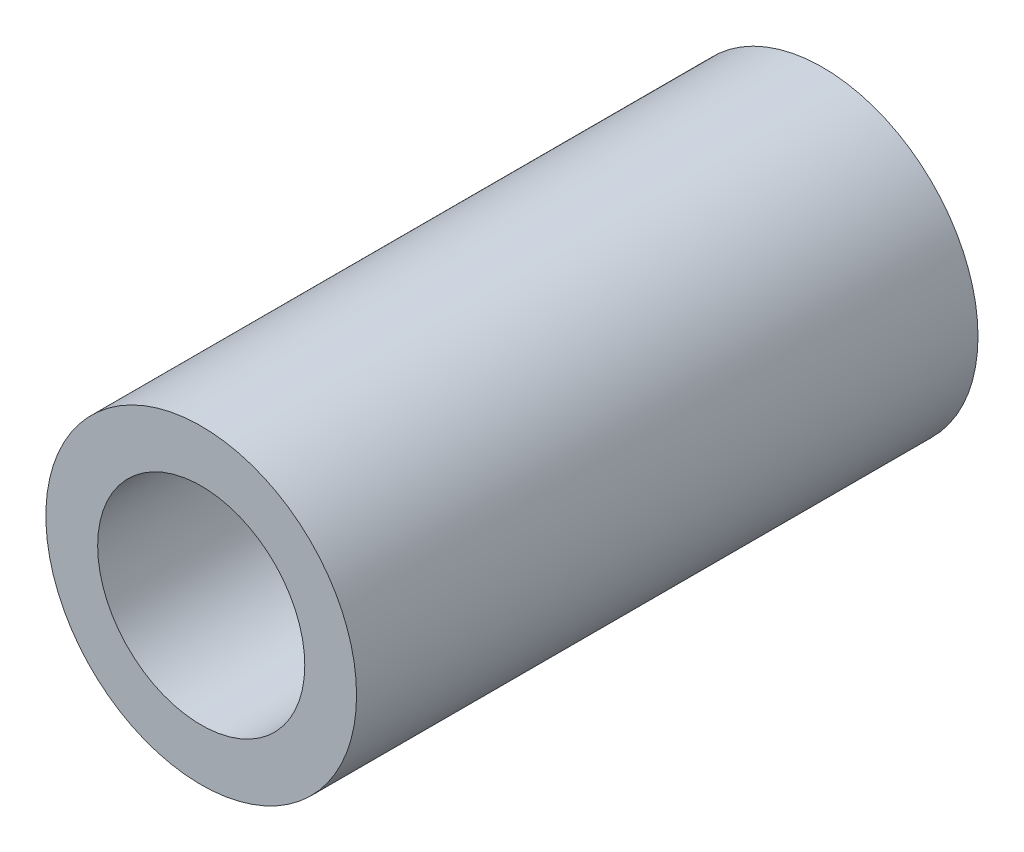
SolidWorks part; units mm, degrees
ref_plane "Plan de face" through (0, 0, 0) normal (0, 0, 1) x (1, 0, 0)
ref_plane "Plan de dessus" through (0, 0, 0) normal (0, 1, 0) x (1, 0, 0)
ref_plane "Plan de droite" through (0, 0, 0) normal (1, 0, 0) x (0, 0, -1)
sketch "Esquisse2" plane through (0, 0, 0) normal (0, 0, 1) x (1, 0, 0)
  circle A0 centre (0, 0) radius 10
  circle A1 centre (0, 0) radius 15
  dimension "D1" = 20
  dimension "D2" = 30
extrude "Boss.-Extru.1" add sketch "Esquisse2" along normal blind 60
